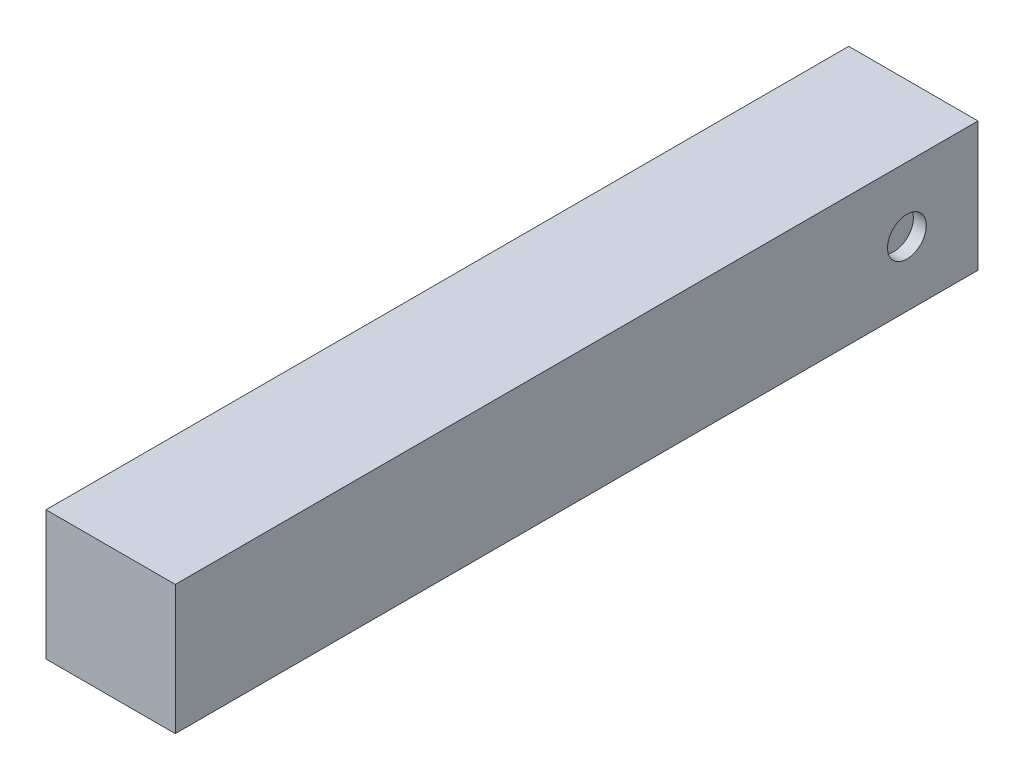
SolidWorks part; units mm, degrees
ref_plane "Front" through (0, 0, 0) normal (0, 0, 1) x (1, 0, 0)
ref_plane "Top" through (0, 0, 0) normal (0, 1, 0) x (1, 0, 0)
ref_plane "Right" through (0, 0, 0) normal (1, 0, 0) x (0, 0, -1)
sketch "草图1" plane through (0, 0, 0) normal (1, 0, 0) x (0, 0, -1)
  line L0 (-14.1759, 10) -> (-14.176, -10)
  line L1 (-14.1759, 10) -> (110, 10)
  line L3 (-14.176, -10) -> (110, -10)
  line L4 (110, 10) -> (110, -10)
  dimension "D2" = 20
  dimension "D3" = 110
  dimension "D4" = 10
extrude "凸台-拉伸1" add sketch "草图1" along normal blind 20
sketch "草图2" plane through (0, 0, -110) normal (0, 0, -1) x (-1, 0, 0)
  circle A0 centre (-10, 0) radius 6
extrude "切除-拉伸1" cut sketch "草图2" against normal blind 80
sketch "草图3" plane through (20, 0, 0) normal (1, 0, 0) x (0, 0, -1)
  line L0 (110, -10) -> (110, 10) construction
  circle A0 centre (99, 0) radius 3
  dimension "D1" = 11
extrude "切除-拉伸2" cut sketch "草图3" against normal blind 2
